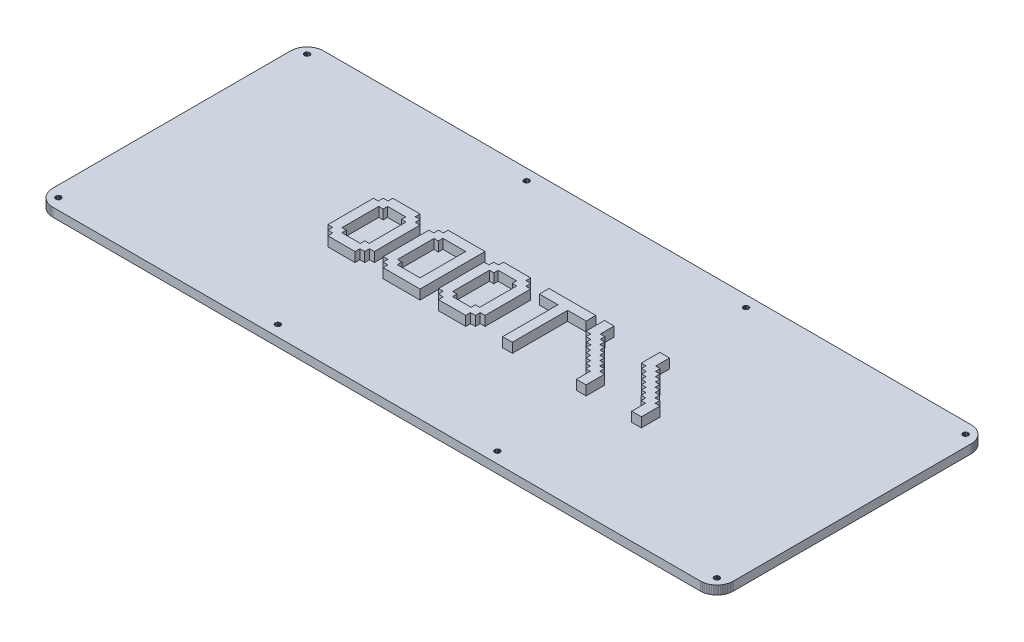
SolidWorks part; units mm, degrees
material "Acrylic (Medium-high impact)"
ref_plane "Front Plane" through (0, 0, 0) normal (0, 0, 1) x (1, 0, 0)
ref_plane "Top Plane" through (0, 0, 0) normal (0, 1, 0) x (1, 0, 0)
ref_plane "Right Plane" through (0, 0, 0) normal (1, 0, 0) x (0, 0, -1)
sketch "Sketch1" plane through (0, 0, 0) normal (0, 1, 0) x (1, 0, 0)
  line L0 (362.807, 147.967) -> (363.513, 147.941)
  line L1 (363.513, 147.941) -> (364.215, 147.857)
  line L2 (364.215, 147.857) -> (364.91, 147.719)
  line L3 (364.91, 147.719) -> (365.591, 147.527)
  line L4 (365.591, 147.527) -> (366.254, 147.282)
  line L5 (366.254, 147.282) -> (366.896, 146.987)
  line L6 (366.896, 146.987) -> (367.51, 146.641)
  line L7 (367.51, 146.641) -> (368.099, 146.25)
  line L8 (368.099, 146.25) -> (368.653, 145.812)
  line L9 (368.653, 145.812) -> (369.171, 145.331)
  line L10 (369.171, 145.331) -> (369.651, 144.812)
  line L11 (369.651, 144.812) -> (370.089, 144.259)
  line L12 (370.089, 144.259) -> (370.48, 143.67)
  line L13 (370.48, 143.67) -> (370.826, 143.053)
  line L14 (370.826, 143.053) -> (371.122, 142.412)
  line L15 (371.122, 142.412) -> (371.369, 141.749)
  line L16 (371.369, 141.749) -> (371.56, 141.07)
  line L17 (371.56, 141.07) -> (371.697, 140.375)
  line L18 (371.697, 140.375) -> (371.778, 139.674)
  line L19 (371.778, 139.674) -> (371.807, 138.967)
  line L20 (371.807, 138.967) -> (371.807, 9.0909)
  line L21 (371.807, 9.0909) -> (371.778, 8.3854)
  line L22 (371.778, 8.3854) -> (371.697, 7.684)
  line L23 (371.697, 7.684) -> (371.56, 6.9908)
  line L24 (371.56, 6.9908) -> (371.369, 6.31)
  line L25 (371.369, 6.31) -> (371.122, 5.6472)
  line L26 (371.122, 5.6472) -> (370.826, 5.0064)
  line L27 (370.826, 5.0064) -> (370.48, 4.3891)
  line L28 (370.48, 4.3891) -> (370.089, 3.8006)
  line L29 (370.089, 3.8006) -> (369.651, 3.2467)
  line L30 (369.651, 3.2467) -> (369.171, 2.7285)
  line L31 (369.171, 2.7285) -> (368.653, 2.2476)
  line L32 (368.653, 2.2476) -> (368.099, 1.8107)
  line L33 (368.099, 1.8107) -> (367.51, 1.418)
  line L34 (367.51, 1.418) -> (366.896, 1.0721)
  line L35 (366.896, 1.0721) -> (366.254, 0.7772)
  line L36 (366.254, 0.7772) -> (365.591, 0.5319)
  line L37 (365.591, 0.5319) -> (364.91, 0.3404)
  line L38 (364.91, 0.3404) -> (364.215, 0.2026)
  line L39 (364.215, 0.2026) -> (363.513, 0.1185)
  line L40 (363.513, 0.1185) -> (362.807, 0.091)
  line L41 (362.807, 0.091) -> (9.0951, 0.091)
  line L42 (9.0951, 0.091) -> (8.3881, 0.1185)
  line L43 (8.3881, 0.1185) -> (7.6867, 0.2026)
  line L44 (7.6867, 0.2026) -> (6.9922, 0.3404)
  line L45 (6.9922, 0.3404) -> (6.3128, 0.5319)
  line L46 (6.3128, 0.5319) -> (5.6499, 0.7772)
  line L47 (5.6499, 0.7772) -> (5.0092, 1.0721)
  line L48 (5.0092, 1.0721) -> (4.3918, 1.418)
  line L49 (4.3918, 1.418) -> (3.8034, 1.8107)
  line L50 (3.8034, 1.8107) -> (3.2494, 2.2476)
  line L51 (3.2494, 2.2476) -> (2.7313, 2.7285)
  line L52 (2.7313, 2.7285) -> (2.2503, 3.2467)
  line L53 (2.2503, 3.2467) -> (1.8121, 3.8006)
  line L54 (1.8121, 3.8006) -> (1.4208, 4.3891)
  line L55 (1.4208, 4.3891) -> (1.0749, 5.0064)
  line L56 (1.0749, 5.0064) -> (0.78, 5.6472)
  line L57 (0.78, 5.6472) -> (0.5347, 6.31)
  line L58 (0.5347, 6.31) -> (0.3431, 6.9908)
  line L59 (0.3431, 6.9908) -> (0.2053, 7.684)
  line L60 (0.2053, 7.684) -> (0.1213, 8.3854)
  line L61 (0.1213, 8.3854) -> (0.0937, 9.0923)
  line L62 (0.0937, 9.0923) -> (0.0951, 138.967)
  line L63 (0.0951, 138.967) -> (0.1213, 139.674)
  line L64 (0.1213, 139.674) -> (0.2053, 140.375)
  line L65 (0.2053, 140.375) -> (0.3431, 141.07)
  line L66 (0.3431, 141.07) -> (0.5347, 141.749)
  line L67 (0.5347, 141.749) -> (0.78, 142.412)
  line L68 (0.78, 142.412) -> (1.0749, 143.053)
  line L69 (1.0749, 143.053) -> (1.4208, 143.67)
  line L70 (1.4208, 143.67) -> (1.8121, 144.259)
  line L71 (1.8121, 144.259) -> (2.2503, 144.812)
  line L72 (2.2503, 144.812) -> (2.7313, 145.331)
  line L73 (2.7313, 145.331) -> (3.2494, 145.812)
  line L74 (3.2494, 145.812) -> (3.8034, 146.25)
  line L75 (3.8034, 146.25) -> (4.3918, 146.641)
  line L76 (4.3918, 146.641) -> (5.0092, 146.987)
  line L77 (5.0092, 146.987) -> (5.6499, 147.282)
  line L78 (5.6499, 147.282) -> (6.3128, 147.527)
  line L79 (6.3128, 147.527) -> (6.9922, 147.719)
  line L80 (6.9922, 147.719) -> (7.6867, 147.857)
  line L81 (7.6867, 147.857) -> (8.3881, 147.941)
  line L82 (8.3881, 147.941) -> (9.0951, 147.968)
  line L83 (9.0951, 147.968) -> (362.807, 147.967)
  line L84 (365.326, 7.5186) -> (364.917, 7.3119)
  line L85 (364.917, 7.3119) -> (364.589, 6.9825)
  line L86 (364.589, 6.9825) -> (364.381, 6.5719)
  line L87 (364.381, 6.5719) -> (364.307, 6.1157)
  line L88 (364.307, 6.1157) -> (364.381, 5.661)
  line L89 (364.381, 5.661) -> (364.589, 5.2503)
  line L90 (364.589, 5.2503) -> (364.917, 4.9237)
  line L91 (364.917, 4.9237) -> (365.326, 4.7143)
  line L92 (365.326, 4.7143) -> (365.781, 4.6413)
  line L93 (365.781, 4.6413) -> (366.24, 4.7143)
  line L94 (366.24, 4.7143) -> (366.649, 4.9237)
  line L95 (366.649, 4.9237) -> (366.977, 5.2503)
  line L96 (366.977, 5.2503) -> (367.185, 5.661)
  line L97 (367.185, 5.661) -> (367.259, 6.1157)
  line L98 (367.259, 6.1157) -> (367.185, 6.5719)
  line L99 (367.185, 6.5719) -> (366.977, 6.9825)
  line L100 (366.977, 6.9825) -> (366.649, 7.3119)
  line L101 (366.649, 7.3119) -> (366.24, 7.5186)
  line L102 (366.24, 7.5186) -> (365.781, 7.5916)
  line L103 (365.781, 7.5916) -> (365.326, 7.5186)
  line L104 (245.438, 7.5186) -> (245.027, 7.3119)
  line L105 (245.027, 7.3119) -> (244.703, 6.9825)
  line L106 (244.703, 6.9825) -> (244.492, 6.5719)
  line L107 (244.492, 6.5719) -> (244.42, 6.1157)
  line L108 (244.42, 6.1157) -> (244.492, 5.661)
  line L109 (244.492, 5.661) -> (244.703, 5.2503)
  line L110 (244.703, 5.2503) -> (245.027, 4.9237)
  line L111 (245.027, 4.9237) -> (245.438, 4.7143)
  line L112 (245.438, 4.7143) -> (245.894, 4.6413)
  line L113 (245.894, 4.6413) -> (246.35, 4.7143)
  line L114 (246.35, 4.7143) -> (246.761, 4.9237)
  line L115 (246.761, 4.9237) -> (247.088, 5.2503)
  line L116 (247.088, 5.2503) -> (247.297, 5.661)
  line L117 (247.297, 5.661) -> (247.37, 6.1157)
  line L118 (247.37, 6.1157) -> (247.297, 6.5719)
  line L119 (247.297, 6.5719) -> (247.088, 6.9825)
  line L120 (247.088, 6.9825) -> (246.761, 7.3119)
  line L121 (246.761, 7.3119) -> (246.35, 7.5186)
  line L122 (246.35, 7.5186) -> (245.894, 7.5916)
  line L123 (245.894, 7.5916) -> (245.438, 7.5186)
  line L124 (125.552, 7.5186) -> (125.138, 7.3119)
  line L125 (125.138, 7.3119) -> (124.815, 6.9825)
  line L126 (124.815, 6.9825) -> (124.604, 6.5719)
  line L127 (124.604, 6.5719) -> (124.532, 6.1157)
  line L128 (124.532, 6.1157) -> (124.604, 5.661)
  line L129 (124.604, 5.661) -> (124.815, 5.2503)
  line L130 (124.815, 5.2503) -> (125.138, 4.9237)
  line L131 (125.138, 4.9237) -> (125.552, 4.7143)
  line L132 (125.552, 4.7143) -> (126.007, 4.6413)
  line L133 (126.007, 4.6413) -> (126.463, 4.7143)
  line L134 (126.463, 4.7143) -> (126.873, 4.9237)
  line L135 (126.873, 4.9237) -> (127.201, 5.2503)
  line L136 (127.201, 5.2503) -> (127.409, 5.661)
  line L137 (127.409, 5.661) -> (127.482, 6.1157)
  line L138 (127.482, 6.1157) -> (127.409, 6.5719)
  line L139 (127.409, 6.5719) -> (127.201, 6.9825)
  line L140 (127.201, 6.9825) -> (126.873, 7.3119)
  line L141 (126.873, 7.3119) -> (126.463, 7.5186)
  line L142 (126.463, 7.5186) -> (126.007, 7.5916)
  line L143 (126.007, 7.5916) -> (125.552, 7.5186)
  line L144 (5.6637, 7.5186) -> (5.2531, 7.3119)
  line L145 (5.2531, 7.3119) -> (4.9251, 6.9825)
  line L146 (4.9251, 6.9825) -> (4.717, 6.5719)
  line L147 (4.717, 6.5719) -> (4.644, 6.1157)
  line L148 (4.644, 6.1157) -> (4.717, 5.661)
  line L149 (4.717, 5.661) -> (4.9251, 5.2503)
  line L150 (4.9251, 5.2503) -> (5.2531, 4.9237)
  line L151 (5.2531, 4.9237) -> (5.6637, 4.7143)
  line L152 (5.6637, 4.7143) -> (6.1185, 4.6413)
  line L153 (6.1185, 4.6413) -> (6.5746, 4.7143)
  line L154 (6.5746, 4.7143) -> (6.9853, 4.9237)
  line L155 (6.9853, 4.9237) -> (7.3133, 5.2503)
  line L156 (7.3133, 5.2503) -> (7.5213, 5.661)
  line L157 (7.5213, 5.661) -> (7.5944, 6.1157)
  line L158 (7.5944, 6.1157) -> (7.5213, 6.5719)
  line L159 (7.5213, 6.5719) -> (7.3133, 6.9825)
  line L160 (7.3133, 6.9825) -> (6.9853, 7.3119)
  line L161 (6.9853, 7.3119) -> (6.5746, 7.5186)
  line L162 (6.5746, 7.5186) -> (6.1185, 7.5916)
  line L163 (6.1185, 7.5916) -> (5.6637, 7.5186)
  line L164 (125.552, 143.345) -> (125.138, 143.137)
  line L165 (125.138, 143.137) -> (124.815, 142.809)
  line L166 (124.815, 142.809) -> (124.604, 142.398)
  line L167 (124.604, 142.398) -> (124.532, 141.942)
  line L168 (124.532, 141.942) -> (124.604, 141.487)
  line L169 (124.604, 141.487) -> (124.815, 141.077)
  line L170 (124.815, 141.077) -> (125.138, 140.75)
  line L171 (125.138, 140.75) -> (125.552, 140.541)
  line L172 (125.552, 140.541) -> (126.007, 140.468)
  line L173 (126.007, 140.468) -> (126.463, 140.541)
  line L174 (126.463, 140.541) -> (126.873, 140.75)
  line L175 (126.873, 140.75) -> (127.201, 141.077)
  line L176 (127.201, 141.077) -> (127.409, 141.487)
  line L177 (127.409, 141.487) -> (127.482, 141.942)
  line L178 (127.482, 141.942) -> (127.409, 142.398)
  line L179 (127.409, 142.398) -> (127.201, 142.809)
  line L180 (127.201, 142.809) -> (126.873, 143.137)
  line L181 (126.873, 143.137) -> (126.463, 143.345)
  line L182 (126.463, 143.345) -> (126.007, 143.417)
  line L183 (126.007, 143.417) -> (125.552, 143.345)
  line L184 (245.438, 143.345) -> (245.027, 143.137)
  line L185 (245.027, 143.137) -> (244.703, 142.809)
  line L186 (244.703, 142.809) -> (244.492, 142.398)
  line L187 (244.492, 142.398) -> (244.42, 141.942)
  line L188 (244.42, 141.942) -> (244.492, 141.487)
  line L189 (244.492, 141.487) -> (244.703, 141.077)
  line L190 (244.703, 141.077) -> (245.027, 140.75)
  line L191 (245.027, 140.75) -> (245.438, 140.541)
  line L192 (245.438, 140.541) -> (245.894, 140.468)
  line L193 (245.894, 140.468) -> (246.35, 140.541)
  line L194 (246.35, 140.541) -> (246.761, 140.75)
  line L195 (246.761, 140.75) -> (247.088, 141.077)
  line L196 (247.088, 141.077) -> (247.297, 141.487)
  line L197 (247.297, 141.487) -> (247.37, 141.942)
  line L198 (247.37, 141.942) -> (247.297, 142.398)
  line L199 (247.297, 142.398) -> (247.088, 142.809)
  line L200 (247.088, 142.809) -> (246.761, 143.137)
  line L201 (246.761, 143.137) -> (246.35, 143.345)
  line L202 (246.35, 143.345) -> (245.894, 143.417)
  line L203 (245.894, 143.417) -> (245.438, 143.345)
  line L204 (365.326, 143.345) -> (364.917, 143.137)
  line L205 (364.917, 143.137) -> (364.589, 142.809)
  line L206 (364.589, 142.809) -> (364.381, 142.398)
  line L207 (364.381, 142.398) -> (364.307, 141.942)
  line L208 (364.307, 141.942) -> (364.381, 141.487)
  line L209 (364.381, 141.487) -> (364.589, 141.077)
  line L210 (364.589, 141.077) -> (364.917, 140.75)
  line L211 (364.917, 140.75) -> (365.326, 140.541)
  line L212 (365.326, 140.541) -> (365.781, 140.468)
  line L213 (365.781, 140.468) -> (366.24, 140.541)
  line L214 (366.24, 140.541) -> (366.649, 140.75)
  line L215 (366.649, 140.75) -> (366.977, 141.077)
  line L216 (366.977, 141.077) -> (367.185, 141.487)
  line L217 (367.185, 141.487) -> (367.259, 141.942)
  line L218 (367.259, 141.942) -> (367.185, 142.398)
  line L219 (367.185, 142.398) -> (366.977, 142.809)
  line L220 (366.977, 142.809) -> (366.649, 143.137)
  line L221 (366.649, 143.137) -> (366.24, 143.345)
  line L222 (366.24, 143.345) -> (365.781, 143.417)
  line L223 (365.781, 143.417) -> (365.326, 143.345)
  line L224 (5.6637, 143.345) -> (5.2531, 143.137)
  line L225 (5.2531, 143.137) -> (4.9251, 142.809)
  line L226 (4.9251, 142.809) -> (4.717, 142.398)
  line L227 (4.717, 142.398) -> (4.644, 141.942)
  line L228 (4.644, 141.942) -> (4.717, 141.487)
  line L229 (4.717, 141.487) -> (4.9251, 141.077)
  line L230 (4.9251, 141.077) -> (5.2531, 140.75)
  line L231 (5.2531, 140.75) -> (5.6637, 140.541)
  line L232 (5.6637, 140.541) -> (6.1185, 140.468)
  line L233 (6.1185, 140.468) -> (6.5746, 140.541)
  line L234 (6.5746, 140.541) -> (6.9853, 140.75)
  line L235 (6.9853, 140.75) -> (7.3133, 141.077)
  line L236 (7.3133, 141.077) -> (7.5213, 141.487)
  line L237 (7.5213, 141.487) -> (7.5944, 141.942)
  line L238 (7.5944, 141.942) -> (7.5213, 142.398)
  line L239 (7.5213, 142.398) -> (7.3133, 142.809)
  line L240 (7.3133, 142.809) -> (6.9853, 143.137)
  line L241 (6.9853, 143.137) -> (6.5746, 143.345)
  line L242 (6.5746, 143.345) -> (6.1185, 143.417)
  line L243 (6.1185, 143.417) -> (5.6637, 143.345)
extrude "Boss-Extrude1" add sketch "Sketch1" along normal blind 4.7625
sketch "Sketch2" plane through (0, 0, 0) normal (0, -1, 0) x (1, 0, 0)
  line L0 (371.807, -74.029) -> (0.0944, -74.0296) construction
  line L1 (371.807, -9.0909) -> (371.807, -138.967) construction
  line L2 (0.0951, -138.967) -> (0.0937, -9.0923) construction
  line L3 (185.951, -147.9675) -> (185.951, -0.091) construction
  line L4 (362.807, -147.967) -> (9.0951, -147.968) construction
  line L5 (9.0951, -0.091) -> (362.807, -0.091) construction
  line L6 (185.9504, -54.0293) -> (185.951, -94.0293) construction
  line L7 (371.8065, -54.0293) -> (0.0942, -54.0293) construction
  text T0 "//TODO" font "VCR OSD Mono" height 35.5
  point P15 (185.9507, -74.0293)
  point P18 (185.9504, -54.0293)
extrude "Boss-Extrude3" add sketch "Sketch2" against normal blind 10
